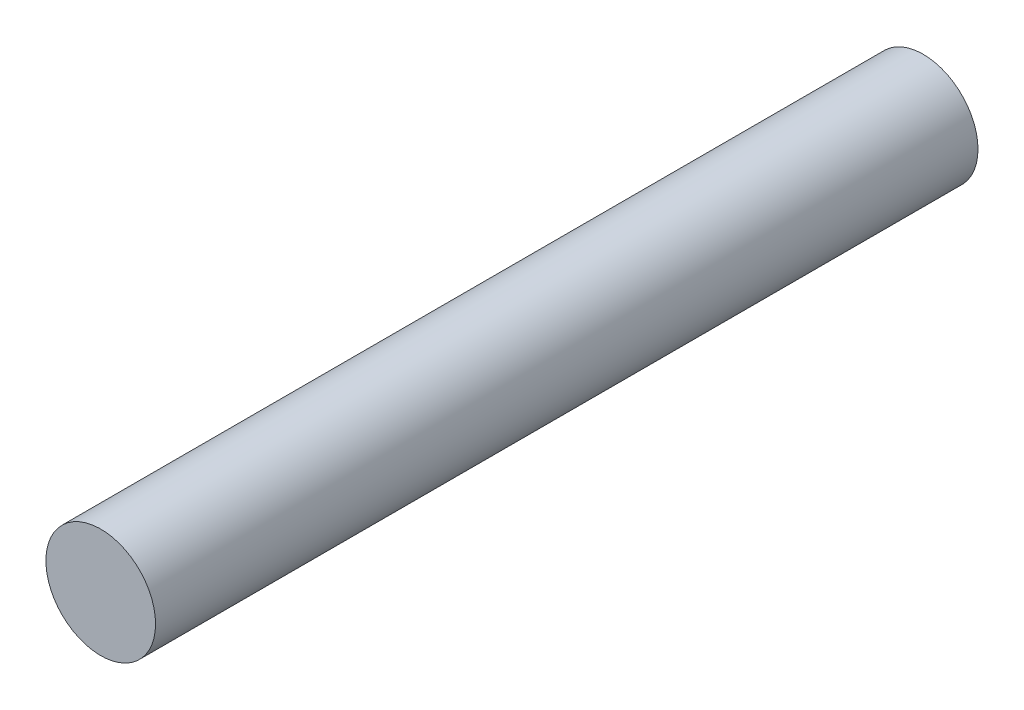
SolidWorks part; units mm, degrees
ref_plane "정면" through (0, 0, 0) normal (0, 0, 1) x (1, 0, 0)
ref_plane "윗면" through (0, 0, 0) normal (0, 1, 0) x (1, 0, 0)
ref_plane "우측면" through (0, 0, 0) normal (1, 0, 0) x (0, 0, -1)
sketch "Sketch1" plane through (0, 0, 0) normal (0, 0, 1) x (1, 0, 0)
  circle A0 centre (0, 0) radius 2.54
  dimension "D1" = 5.08
extrude "Extrude1" add sketch "Sketch1" along normal blind 38.1
